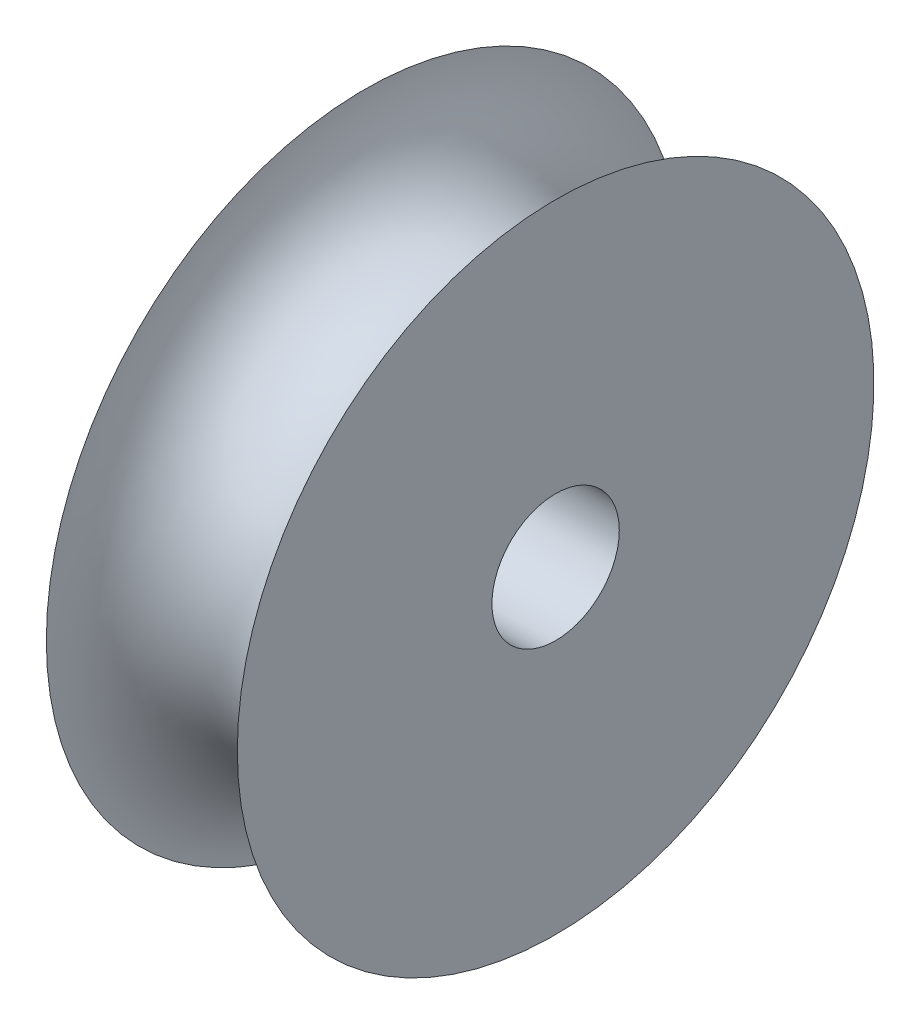
SolidWorks part; units mm, degrees
ref_plane "Front Plane" through (0, 0, 0) normal (0, 0, 1) x (1, 0, 0)
ref_plane "Top Plane" through (0, 0, 0) normal (0, 1, 0) x (1, 0, 0)
ref_plane "Right Plane" through (0, 0, 0) normal (1, 0, 0) x (0, 0, -1)
sketch "Sketch1" plane through (0, 0, 0) normal (0, 0, 1) x (1, 0, 0)
  line L0 (0, 15.875) -> (0, 0)
  line L1 (0, 0) -> (9.525, 0)
  line L2 (9.525, 0) -> (9.525, 15.875)
  arc A0 (0, 15.875) -> (9.525, 15.875) centre (4.7625, 15.875) ccw
  dimension "D1" = 15.875
  dimension "D2" = 9.525
revolve "Revolve1" add sketch "Sketch1" angle 360 about L1
sketch "Sketch2" plane through (9.525, 0, 0) normal (1, 0, 0) x (0, 0, -1)
  circle A0 centre (0, 0) radius 3.175
  dimension "D1" = 6.35
extrude "Cut-Extrude1" cut sketch "Sketch2" against normal through all
